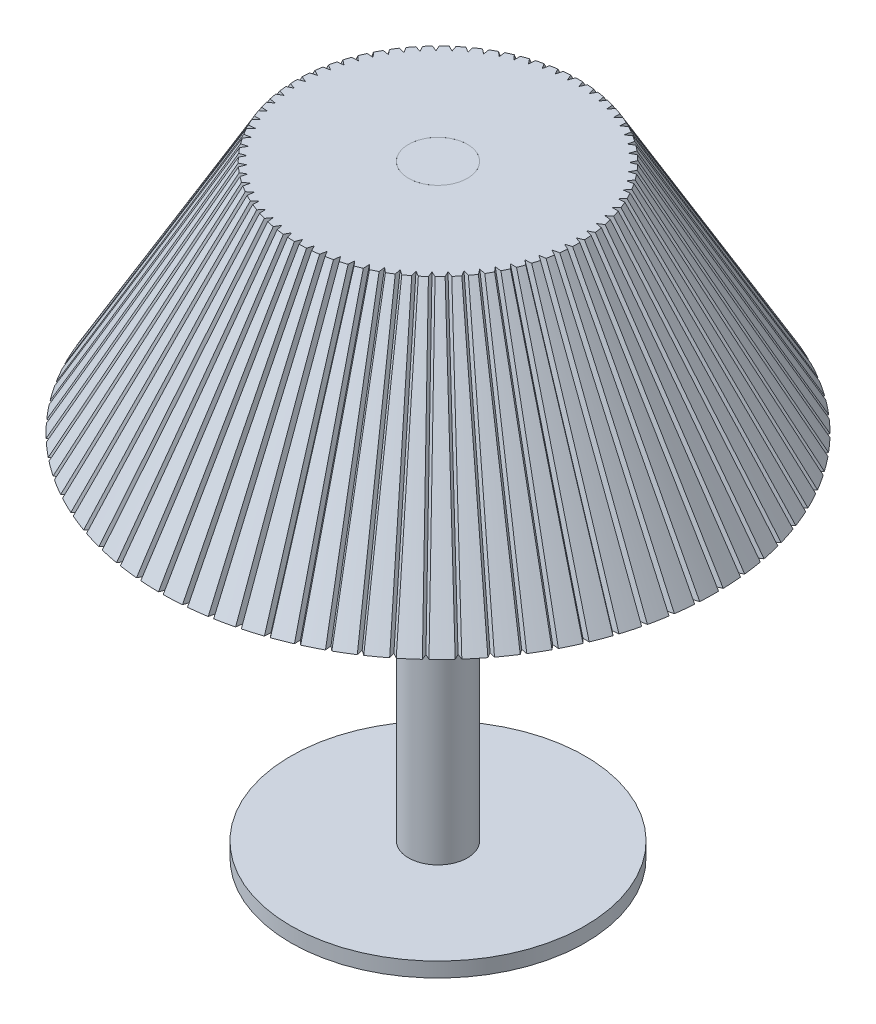
SolidWorks part; units mm, degrees
ref_plane "Front Plane" through (0, 0, 0) normal (0, 0, 1) x (1, 0, 0)
ref_plane "Top Plane" through (0, 0, 0) normal (0, 1, 0) x (1, 0, 0)
ref_plane "Right Plane" through (0, 0, 0) normal (1, 0, 0) x (0, 0, -1)
sketch "Sketch1" plane through (0, 0, 0) normal (0, 1, 0) x (1, 0, 0)
  circle A0 centre (0, 0) radius 25
  dimension "D1" = 50
extrude "Boss-Extrude1" add sketch "Sketch1" along normal blind 2.5
sketch "Sketch2" plane through (0, 2.5, 0) normal (0, 1, 0) x (1, 0, 0)
  circle A0 centre (0, 0) radius 5
  dimension "D1" = 10
extrude "Boss-Extrude2" add sketch "Sketch2" along normal blind 100
ref_axis "Axis1" through (0, -5.125, 0) along (0, 1, 0)
sketch "Sketch3" plane through (0, 0, 0) normal (0, 0, 1) x (1, 0, 0)
  line L0 (20, 102.5) -> (24, 102.5)
  line L1 (24, 102.5) -> (47.094, 62.5)
  line L2 (47.094, 62.5) -> (42.5167, 62.5)
  line L3 (42.5167, 62.5) -> (20, 101.5)
  line L4 (5, 102.5) -> (-5, 102.5) construction
  line L5 (20, 102.5) -> (5, 102.5)
  line L6 (5, 102.5) -> (5, 101.5)
  line L7 (5, 2.5) -> (5, 102.5) construction
  line L8 (5, 101.5) -> (20, 101.5)
  point P12 (23.0868, 101.5)
  point P13 (0, 0)
  point P14 (6.5034, 102.5)
  dimension "D1" = 15
  dimension "D2" = 4
  dimension "D3" = 60
  dimension "D4" = 40
  dimension "D5" = 1
revolve "Revolve1" add sketch "Sketch3" angle 360 about axis through (0, -5.125, 0) along (0, 1, 0)
ref_plane "Plane1" through (0, 36.0173, 62.3838) normal (0, 0.5, 0.866) x (1, 0, 0)
sketch "Sketch4" plane through (0, 36.0173, 62.3838) normal (0, 0.5, 0.866) x (1, 0, 0)
  line L0 (0, 30.5796) -> (0, 76.7676)
  line L2 (0, -4.4384) -> (0, 93.206) construction
  ellipse E0 centre (0, 88.7676) end of major axis (-24, 88.7676) minor radius 12 construction
  ellipse E1 centre (0, 54.1266) end of major axis (-47.094, 54.1266) minor radius 23.547 construction
  point P2 (0, 0)
  point P9 (0, 0)
sketch "Sketch9" plane through (0, 102.5, 0) normal (0, 1, 0) x (1, 0, 0)
  line L0 (0, -23) -> (-1, -25.5)
  line L1 (-1, -25.5) -> (1, -25.5)
  line L2 (1, -25.5) -> (0, -23)
  line L3 (0, -47.094) -> (0, -24) construction
  point P2 (0, -25.5)
  point P6 (0, 0)
  dimension "D1" = 2
  dimension "D2" = 1
  dimension "D3" = 1.5
sweep "Cut-Sweep2" cut profiles "Sketch9" path "Sketch4"
pattern_circular "CirPattern1" count 75 over 360 about axis through (0, 0, 0) along (0, 1, 0) of "Cut-Sweep2"
